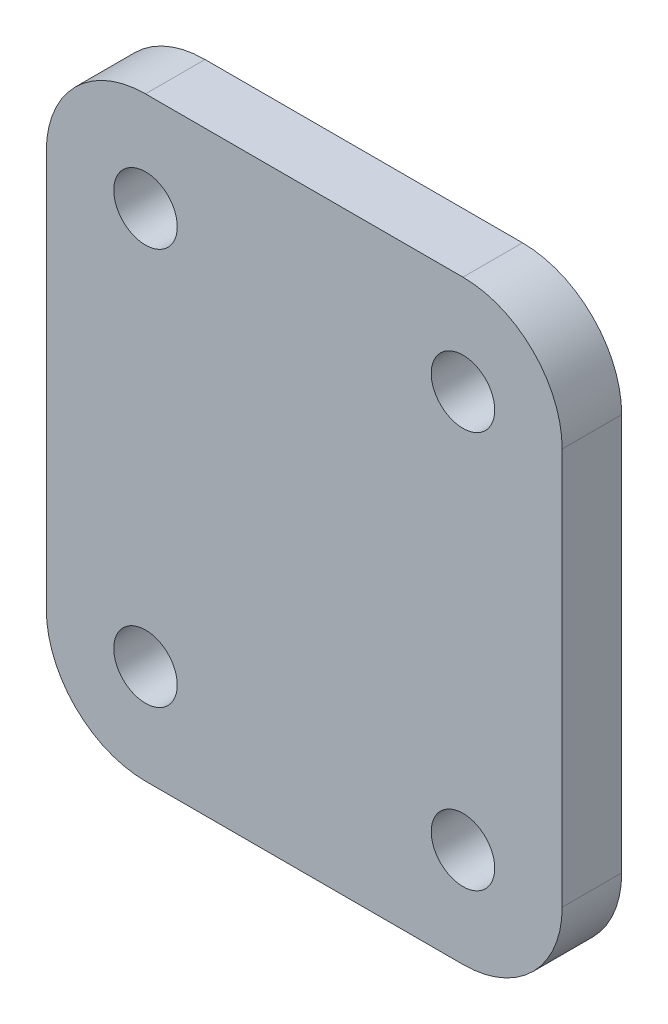
SolidWorks part; units mm, degrees
material "Acrílico (médio-alto impacto)"
ref_plane "Plano frontal" through (0, 0, 0) normal (0, 0, 1) x (1, 0, 0)
ref_plane "Plano superior" through (0, 0, 0) normal (0, 1, 0) x (1, 0, 0)
ref_plane "Plano direito" through (0, 0, 0) normal (1, 0, 0) x (0, 0, -1)
sketch "Esboço1" plane through (0, 0, 0) normal (0, 0, 1) x (1, 0, 0)
  line L1 (-13, -15) -> (13, -15)
  line L2 (-13, -15) -> (-13, 15)
  line L3 (-13, 15) -> (13, 15)
  line L4 (13, -15) -> (13, 15)
  line L5 (0, 15) -> (0, -15) construction
  line L6 (-13, 0) -> (13, 0) construction
  circle A0 centre (-8, 10) radius 1.6
  circle A2 centre (8, 10) radius 1.6
  circle A3 centre (8, -10) radius 1.6
  circle A4 centre (-8, -10) radius 1.6
  circle A5 centre (0, 0) radius 3.5 construction
  point P0 (0, 0)
  dimension "D1" = 16
  dimension "D2" = 20
  dimension "D3" = 5
  dimension "D5" = 3.2
  dimension "D6" = 7
  dimension "D4" = 5
extrude "Ressalto-extrusão1" add sketch "Esboço1" along normal blind 3 contours L1 L4 L3 L2 A5 A2 A0 A3 A4
fillet "Filete1" radius 5 4 edges at (-13, -15, 1.5) (13, -15, 1.5) (-13, 15, 1.5) (13, 15, 1.5)
